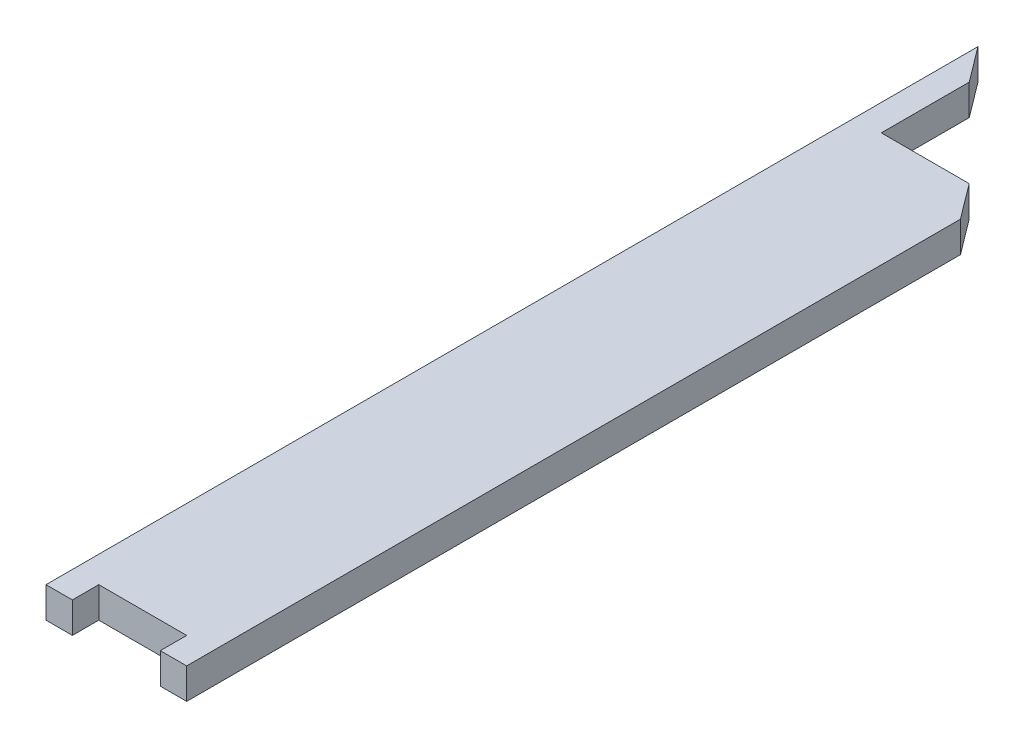
SolidWorks part; units mm, degrees
ref_plane "前视基准面" through (0, 0, 0) normal (0, 0, 1) x (1, 0, 0)
ref_plane "上视基准面" through (0, 0, 0) normal (0, 1, 0) x (1, 0, 0)
ref_plane "右视基准面" through (0, 0, 0) normal (1, 0, 0) x (0, 0, -1)
sketch "草图1" plane through (0, 0, 0) normal (0, 1, 0) x (1, 0, 0)
  line L0 (236.6976, -27.1733) -> (176.6976, -27.1733)
  line L2 (-83.3024, 2092.8267) -> (-83.3024, -27.1733)
  line L3 (-83.3024, -27.1733) -> (-23.3024, -27.1733)
  line L4 (236.6976, 1732.8267) -> (236.6976, -27.1733)
  line L5 (176.6976, -27.1733) -> (176.6976, 32.8267)
  line L8 (176.6976, 32.8267) -> (-23.3024, 32.8267)
  line L9 (-23.3024, 32.8267) -> (-23.3024, -27.1733)
  line L12 (-83.3024, 2092.8267) -> (-23.3024, 2012.8267)
  line L15 (-23.3024, 2012.8267) -> (-23.3024, 1812.8267)
  line L16 (-23.3024, 1812.8267) -> (176.6976, 1812.8267)
  line L19 (236.6976, 1732.8267) -> (176.6976, 1812.8267)
extrude "凸台-拉伸1" add sketch "草图1" along normal blind 70
